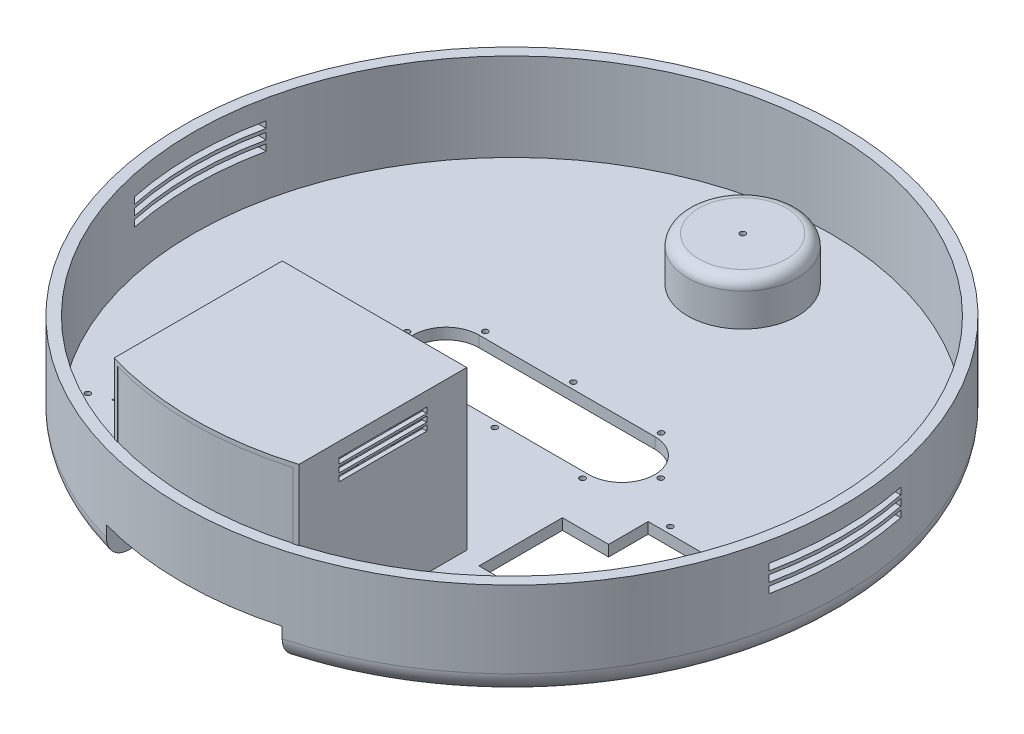
SolidWorks part; units mm, degrees
ref_plane "Front Plane" through (0, 0, 0) normal (0, 0, 1) x (1, 0, 0)
ref_plane "Top Plane" through (0, 0, 0) normal (0, 1, 0) x (1, 0, 0)
ref_plane "Right Plane" through (0, 0, 0) normal (1, 0, 0) x (0, 0, -1)
sketch "Sketch1" plane through (0, 0, 0) normal (0, 1, 0) x (1, 0, 0)
  circle A0 centre (0, 0) radius 150
  dimension "D1" = 300
extrude "Boss-Extrude1" add sketch "Sketch1" along normal blind 45
shell "Shell1" thickness 5
sketch "Sketch2" plane through (0, 5, 0) normal (0, 1, 0) x (1, 0, 0)
  line L0 (0, 177.7581) -> (0, -174.9552) construction
  line L1 (-190.4374, 0) -> (185.8852, 0) construction
  line L10 (72, -84) -> (72, -10)
  line L11 (-98, -84) -> (-72, -84)
  line L12 (-98, -84) -> (-98, -10)
  line L13 (-98, -10) -> (-72, -10)
  line L14 (-72, -84) -> (-72, -10)
  line L15 (98, -10) -> (72, -10)
  line L16 (98, -84) -> (98, -10)
  line L17 (98, -84) -> (72, -84)
  point P9 (-85, -10)
  dimension "D1" = 26
  dimension "D2" = 74
  dimension "D3" = 10
  dimension "D4" = 85
extrude "Cut-Extrude1" cut sketch "Sketch2" against normal through all both and the other way through all
sketch "Sketch3" plane through (0, 5, 0) normal (0, 1, 0) x (1, 0, 0)
  line L0 (0, 188.3464) -> (0, -168.3464) construction
  line L1 (-169.6656, 0) -> (175.3341, 0) construction
  line L2 (-40, 10) -> (40, 10) construction
  line L23 (-40, 25) -> (40, 25)
  line L24 (-40, -5) -> (40, -5)
  line L25 (-40, 29.6333) -> (40, 29.6333) construction
  line L26 (-40, -9.6333) -> (40, -9.6333) construction
  line L27 (-68.6194, 10) -> (61.5175, 10) construction
  line L28 (-72, -10) -> (-98, -10) construction
  line L30 (-117.2427, -47) -> (-55.0904, -47) construction
  line L31 (117.2427, -47) -> (55.0904, -47) construction
  line L32 (-72, -84) -> (-72, -10) construction
  arc A4 (-40, 25) -> (-40, -5) centre (-40, 10) ccw
  arc A5 (40, -5) -> (40, 25) centre (40, 10) ccw
  arc A6 (40, -9.6333) -> (40, 29.6333) centre (40, 10) ccw construction
  arc A7 (-40, 29.6333) -> (-40, -9.6333) centre (-40, 10) ccw construction
  circle A8 centre (0, 27.8833) radius 1.25
  circle A9 centre (-57.75, 10) radius 1.25
  circle A10 centre (-40, 27.8833) radius 1.25
  circle A11 centre (40, 27.8833) radius 1.25
  circle A12 centre (40, -7.8833) radius 1.25
  circle A13 centre (0, -7.8833) radius 1.25
  circle A14 centre (-40, -7.8833) radius 1.25
  circle A15 centre (57.75, 10) radius 1.25
  circle A16 centre (-106, -6.9265) radius 1.25
  circle A17 centre (-79, -6.9265) radius 1.25
  circle A18 centre (-79, -87.0734) radius 1.25
  circle A19 centre (-106, -87.0734) radius 1.25
  circle A20 centre (106, -87.0734) radius 1.25
  circle A21 centre (79, -87.0734) radius 1.25
  circle A22 centre (79, -6.9265) radius 1.25
  circle A23 centre (106, -6.9265) radius 1.25
  point P15 (0, 10)
  dimension "D2" = 2.5
  dimension "D8" = 2.5
  dimension "D3" = 80
  dimension "D4" = 30
  dimension "D5" = 10
  dimension "D6" = 1.75
  dimension "D7" = 17.75
  dimension "D9" = 7
  dimension "D10" = 27
  dimension "D12" = 3.0734
  dimension "D1" = 4.6333
extrude "Cut-Extrude2" cut sketch "Sketch3" against normal through all and the other way through all
fillet "Fillet5" radius 10 1 edges at (0, 0, 150)
sketch "Sketch12" plane through (0, 5, 0) normal (0, 1, 0) x (1, 0, 0)
  line L0 (74.5, -61.5) -> (74.5, -100)
  line L1 (52.5, -19) -> (68.5, -19)
  line L2 (74.5, -61.5) -> (68.5, -61.5)
  line L3 (68.5, -61.5) -> (68.5, -51.5)
  line L5 (52.5, -19) -> (52.5, -61.5)
  line L6 (52.5, -61.5) -> (46.5, -61.5)
  line L7 (46.5, -61.5) -> (46.5, -100)
  line L8 (46.5, -100) -> (74.5, -100)
  line L9 (68.5, -42.5) -> (75, -42.5)
  line L10 (72, -84) -> (98, -84)
  line L11 (75, -42.5) -> (75, -51.5)
  line L12 (75, -51.5) -> (68.5, -51.5)
  line L13 (98, -84) -> (98, -10)
  line L14 (68.5, -42.5) -> (68.5, -19)
  line L15 (98, -10) -> (72, -10)
  line L16 (72, -10) -> (72, -84)
  line L17 (14.1942, -47) -> (56.6102, -47) construction
  line L18 (56.6102, -47) -> (112.9835, -47) construction
  line L19 (77, -15) -> (77, -79)
  line L20 (77, -79) -> (93, -79)
  line L21 (93, -79) -> (93, -15)
  line L22 (93, -15) -> (77, -15)
  line L23 (0, 169.9011) -> (0, -188.9418) construction
  line L24 (-56.6102, -47) -> (-112.9835, -47) construction
  line L25 (-14.1942, -47) -> (-56.6102, -47) construction
  line L26 (-93, -15) -> (-77, -15)
  line L27 (-93, -79) -> (-93, -15)
  line L28 (-77, -79) -> (-93, -79)
  line L29 (-77, -15) -> (-77, -79)
  line L30 (-72, -10) -> (-72, -84)
  line L31 (-98, -10) -> (-72, -10)
  line L32 (-68.5, -42.5) -> (-68.5, -19)
  line L33 (-98, -84) -> (-98, -10)
  line L34 (-75, -51.5) -> (-68.5, -51.5)
  line L35 (-75, -42.5) -> (-75, -51.5)
  line L36 (-72, -84) -> (-98, -84)
  line L37 (-68.5, -42.5) -> (-75, -42.5)
  line L38 (-46.5, -100) -> (-74.5, -100)
  line L39 (-46.5, -61.5) -> (-46.5, -100)
  line L40 (-52.5, -61.5) -> (-46.5, -61.5)
  line L41 (-52.5, -19) -> (-52.5, -61.5)
  line L42 (-68.5, -61.5) -> (-68.5, -51.5)
  line L43 (-74.5, -61.5) -> (-68.5, -61.5)
  line L44 (-52.5, -19) -> (-68.5, -19)
  line L45 (-74.5, -61.5) -> (-74.5, -100)
  dimension "D1" = 16
  dimension "D2" = 23.5
  dimension "D3" = 9
  dimension "D4" = 10
  dimension "D5" = 38.5
  dimension "D6" = 28
  dimension "D7" = 38.5
  dimension "D8" = 6
  dimension "D9" = 6.5
  dimension "D10" = 4.5
  dimension "D11" = 37
  dimension "D13" = 8.5
  dimension "D12" = 5
sketch "Sketch13" plane through (0, 0, 0) normal (0, -1, 0) x (1, 0, 0)
  line L6 (14.1942, 47) -> (56.6102, 47) construction
  line L11 (72, 66) -> (50.98, 66)
  line L12 (50.98, 66) -> (50.98, 28)
  line L13 (50.98, 28) -> (72, 28)
  line L15 (56.6102, 47) -> (112.9835, 47) construction
  line L18 (72, 28) -> (72, 66)
  line L19 (72, 10) -> (72, 84) construction
  dimension "D1" = 21.02
  dimension "D2" = 19
  dimension "D3" = 19
extrude "Cut-Extrude5" cut sketch "Sketch13" against normal through all both and the other way through all
mirror "Mirror2" about plane through (0, 0, 0) normal (1, 0, 0) of "Cut-Extrude5"
sketch "Sketch14" plane through (0, 5, 0) normal (0, 1, 0) x (1, 0, 0)
  line L0 (40, 25) -> (-40, 25) construction
  circle A0 centre (0, 105) radius 20
  dimension "D2" = 40
  dimension "D1" = 80
extrude "Cut-Extrude6" cut sketch "Sketch14" against normal through all both and the other way through all
sketch "Sketch15" plane through (0, 5, 0) normal (0, 1, 0) x (1, 0, 0)
  circle A1 centre (0, 105) radius 25
  dimension "D1" = 50
extrude "Boss-Extrude3" add sketch "Sketch15" along normal blind 20
sketch "Sketch16" plane through (0, 5, 0) normal (0, -1, 0) x (1, 0, 0)
  circle A0 centre (0, -105) radius 20
  dimension "D1" = 40
extrude "Cut-Extrude7" cut sketch "Sketch16" against normal blind 15
sketch "Sketch21" plane through (0, 5, 0) normal (0, 1, 0) x (1, 0, 0)
  line L0 (0, 46.2314) -> (0, -166.0702) construction
  line L4 (-40, -144.5683) -> (-40, -64.5683)
  line L5 (-40, -64.5683) -> (40, -64.5683)
  line L6 (40, -144.5683) -> (40, -64.5683)
  circle A1 centre (0, 0) radius 150 construction
  arc A2 (-40, -144.5683) -> (40, -144.5683) centre (0, 0) ccw
  point P11 (0, -64.5683)
  dimension "D2" = 80
  dimension "D1" = 80
extrude "Cut-Extrude8" cut sketch "Sketch21" along normal blind 10 and the other way through all
fillet "Fillet7" radius 5 2 edges at (0, 25, -80) (0, 20, -125)
sketch "Sketch23" plane through (0, 5, 0) normal (0, 1, 0) x (1, 0, 0)
  line L0 (-40, -64.5683) -> (-40, -139.5683)
  line L1 (-40, -64.5683) -> (-40, -139.3736) construction
  line L2 (40, -64.5683) -> (40, -139.5683)
  line L3 (-40, -64.5683) -> (-40, -144.5683)
  line L4 (40, -64.5683) -> (-40, -64.5683)
  line L5 (40, -144.5683) -> (40, -64.5683)
  line L7 (40, -64.5683) -> (-40, -64.5683)
  line L8 (40, -139.3736) -> (40, -64.5683) construction
  line L9 (42, -62.5683) -> (42, -138.9796)
  line L10 (42, -62.5683) -> (-42, -62.5683)
  line L11 (-42, -62.5683) -> (-42, -138.9796)
  line L12 (-42, -62.5683) -> (-42, -139.5683) construction
  line L13 (42, -62.5683) -> (42, -139.5683) construction
  arc A0 (-42, -138.9796) -> (-40, -139.5683) centre (0, 0) ccw
  arc A1 (-40, -144.5683) -> (40, -144.5683) centre (0, 0) ccw
  arc A2 (40, -139.5683) -> (42, -138.9796) centre (0, 0) ccw
  dimension "D2" = 75
  dimension "D1" = 0
  dimension "D4" = 2
extrude "Boss-Extrude4" add sketch "Sketch23" along normal blind 70
sketch "Sketch26" plane through (0, 75, 0) normal (0, 1, 0) x (1, 0, 0)
  line L0 (-40, -137.2917) -> (-40, -139.3736)
  line L2 (40, -137.2917) -> (40, -139.3736)
  arc A0 (-40, -139.3736) -> (40, -139.3736) centre (0, 0) ccw
  arc A1 (-40, -137.2917) -> (40, -137.2917) centre (0, 0) ccw
  circle A2 centre (0, 0) radius 143 construction
  circle A3 centre (0, 0) radius 145 construction
  dimension "D1" = 2
extrude "Boss-Extrude7" add sketch "Sketch26" against normal blind 60
sketch "Sketch27" plane through (0, 75, 0) normal (0, 1, 0) x (1, 0, 0)
  line L0 (-42, -138.9796) -> (-42, -62.5683)
  line L1 (-42, -62.5683) -> (42, -62.5683)
  line L2 (42, -62.5683) -> (42, -138.9796)
  arc A0 (-42, -138.9796) -> (42, -138.9796) centre (0, 0) ccw
extrude "Boss-Extrude8" add sketch "Sketch27" along normal blind 2
sketch "Sketch29" plane through (0, 25, 0) normal (0, 1, 0) x (1, 0, 0)
  circle A0 centre (0, 105) radius 1.25
  dimension "D1" = 2.5
extrude "Cut-Extrude9" cut sketch "Sketch29" against normal through all both and the other way through all
sketch "Sketch30" plane through (0, 0, 62.5683) normal (0, 0, -1) x (-1, 0, 0)
  line L0 (42, 77) -> (42, 5) construction
  line L1 (-42, 5) -> (42, 5) construction
  line L2 (-22.3931, 31.25) -> (31.0689, 31.25) construction
  line L3 (5, 55.7489) -> (5, 12.9965) construction
  circle A0 centre (5, 31.25) radius 15
  circle A1 centre (5, 48) radius 1.25
  circle A2 centre (21.75, 31.25) radius 1.25
  circle A3 centre (-11.75, 31.25) radius 1.25
  circle A4 centre (5, 14.5) radius 1.25
  dimension "D2" = 30
  dimension "D6" = 2.5
  dimension "D7" = 2.5
  dimension "D1" = 26.25
  dimension "D3" = 37
  dimension "D4" = 16.75
  dimension "D5" = 16.75
extrude "Cut-Extrude10" cut sketch "Sketch30" against normal up to surface (2 mm away) up to face at (0, 37.5, 64.5683)
sketch "Sketch31" plane through (42, 0, 0) normal (1, 0, 0) x (0, 0, -1)
  line L0 (-138.9796, 77) -> (-62.5683, 77) construction
  line L1 (-120.7733, 68) -> (-80.7733, 68)
  line L2 (-120.7733, 68) -> (-120.7733, 70.5)
  line L3 (-120.7733, 70.5) -> (-80.7733, 70.5)
  line L4 (-80.7733, 68) -> (-80.7733, 70.5)
  line L5 (-120.7733, 68) -> (-80.7733, 70.5) construction
  line L6 (-120.7733, 70.5) -> (-80.7733, 68) construction
  line L9 (-62.5683, 77) -> (-62.5683, 5) construction
  line L11 (-120.7733, 64.5004) -> (-80.7733, 64.5004)
  line L12 (-120.7733, 64.5004) -> (-120.7733, 66.9996)
  line L13 (-120.7733, 66.9996) -> (-80.7733, 66.9996)
  line L14 (-80.7733, 64.5004) -> (-80.7733, 66.9996)
  line L15 (-120.7733, 64.5004) -> (-80.7733, 66.9996) construction
  line L16 (-120.7733, 66.9996) -> (-80.7733, 64.5004) construction
  line L17 (-120.7733, 61) -> (-80.7733, 61)
  line L18 (-120.7733, 61) -> (-120.7733, 63.5)
  line L19 (-120.7733, 63.5) -> (-80.7733, 63.5)
  line L20 (-80.7733, 61) -> (-80.7733, 63.5)
  line L21 (-120.7733, 61) -> (-80.7733, 63.5) construction
  line L22 (-120.7733, 63.5) -> (-80.7733, 61) construction
  point P0 (-100.7733, 69.25)
  point P9 (-100.7733, 65.75)
  point P14 (-100.7733, 62.25)
  dimension "D1" = 7.75
  dimension "D2" = 40
  dimension "D3" = 2.5
  dimension "D4" = 38.205
  dimension "D5" = 40
  dimension "D6" = 2.4993
  dimension "D7" = 3.5
  dimension "D8" = 40
  dimension "D9" = 2.5
  dimension "D10" = 3.5
extrude "Cut-Extrude11" cut sketch "Sketch31" against normal through all both and the other way through all
sketch "Sketch32" plane through (0, 0, 0) normal (1, 0, 0) x (0, 0, -1)
  line L0 (-30, 24) -> (30, 24)
  line L1 (-30, 24) -> (-30, 27)
  line L2 (-30, 27) -> (30, 27)
  line L3 (30, 24) -> (30, 27)
  line L4 (-30, 24) -> (30, 27) construction
  line L5 (-30, 27) -> (30, 24) construction
  line L6 (-30, 31.5) -> (30, 31.5)
  line L7 (-30, 31.5) -> (-30, 28.5)
  line L8 (-30, 28.5) -> (30, 28.5)
  line L9 (30, 31.5) -> (30, 28.5)
  line L10 (-30, 31.5) -> (30, 28.5) construction
  line L11 (-30, 28.5) -> (30, 31.5) construction
  line L12 (-30, 36) -> (30, 36)
  line L13 (145, 45) -> (-138.784, 45) construction
  line L14 (-30, 36) -> (-30, 33)
  line L15 (-30, 33) -> (30, 33)
  line L16 (30, 36) -> (30, 33)
  line L17 (-30, 36) -> (30, 33) construction
  line L18 (-30, 33) -> (30, 36) construction
  point P0 (0, 25.5)
  point P5 (0, 30)
  point P10 (0, 34.5)
  dimension "D1" = 60
  dimension "D2" = 3
  dimension "D3" = 3
  dimension "D4" = 3
  dimension "D5" = 15
  dimension "D6" = 1.5
extrude "Cut-Extrude12" cut sketch "Sketch32" against normal through all both and the other way through all
